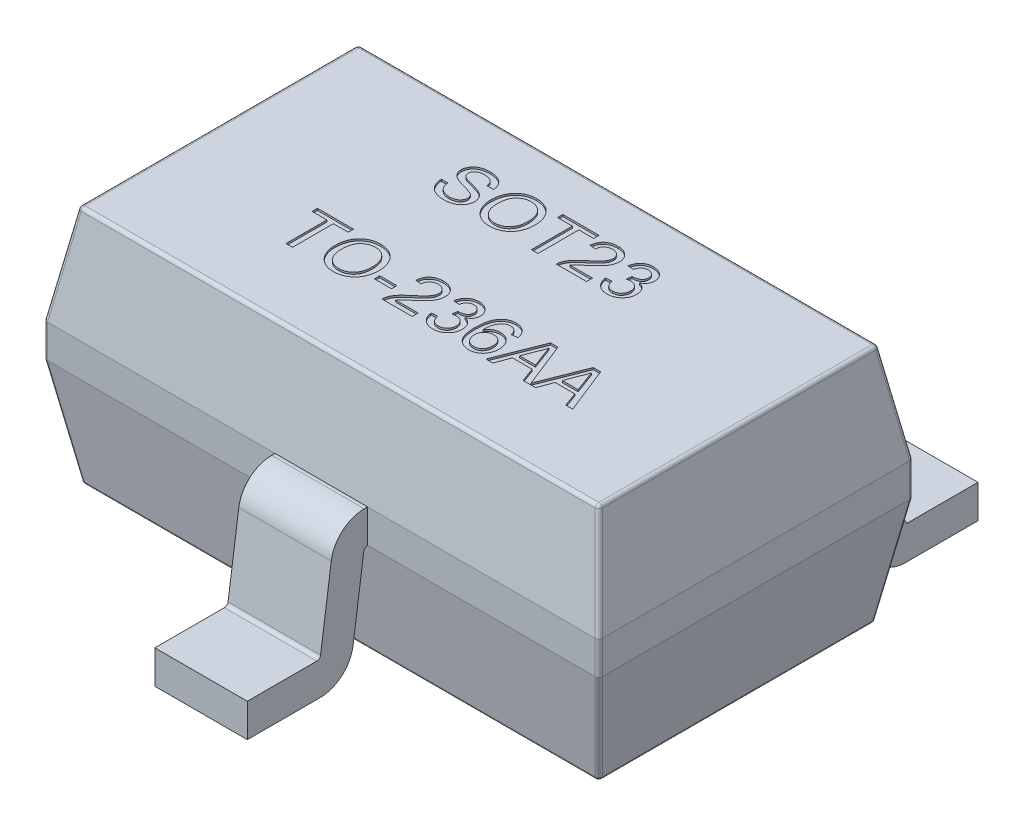
SolidWorks part; units mm, degrees
ref_plane "Front" through (0, 0, 0) normal (0, 0, 1) x (1, 0, 0)
ref_plane "Top" through (0, 0, 0) normal (0, 1, 0) x (1, 0, 0)
ref_plane "Right" through (0, 0, 0) normal (1, 0, 0) x (0, 0, -1)
ref_plane "Plane3" through (0, 0.585, 0) normal (0, 1, 0) x (-1, 0, 0)
sketch "Sketch5" plane through (0, 0.585, 0) normal (0, 1, 0) x (-1, 0, 0)
  line L0 (1.5, -0.85) -> (1.5, 0.85)
  line L1 (0, 0) -> (-1.5, 0) construction
  line L2 (0, 0) -> (0, 0.85) construction
  line L3 (1.5, 0.85) -> (-1.5, 0.85)
  line L4 (-1.5, -0.85) -> (-1.5, 0.85)
  line L5 (1.5, -0.85) -> (-1.5, -0.85)
  point P8 (1.5, 0)
  dimension "D1" = 1.5
  dimension "D2" = 0.85
extrude "Boss-Extrude3" add sketch "Sketch5" against normal blind 0.585 draft 10
sketch "Sketch6" plane through (0, 0.585, 0) normal (0, 1, 0) x (1, 0, 0)
  line L4 (1.5, -0.85) -> (1.5, 0.85)
  line L5 (1.5, 0.85) -> (-1.5, 0.85)
  line L6 (-1.5, 0.85) -> (-1.5, -0.85)
  line L7 (-1.5, -0.85) -> (1.5, -0.85)
  line L8 (1.5, -0.85) -> (1.5, 0.85)
  line L9 (1.5, 0.85) -> (-1.5, 0.85)
  line L10 (-1.5, 0.85) -> (-1.5, -0.85)
  line L11 (-1.5, -0.85) -> (1.5, -0.85)
  dimension "D1" = 0
extrude "Boss-Extrude4" add sketch "Sketch6" along normal blind 0.18
sketch "Sketch7" plane through (0, 0.765, 0) normal (0, 1, 0) x (1, 0, 0)
  line L4 (-1.5, -0.85) -> (1.5, -0.85)
  line L5 (1.5, -0.85) -> (1.5, 0.85)
  line L6 (1.5, 0.85) -> (-1.5, 0.85)
  line L7 (-1.5, 0.85) -> (-1.5, -0.85)
  line L8 (-1.5, -0.85) -> (1.5, -0.85)
  line L9 (1.5, -0.85) -> (1.5, 0.85)
  line L10 (1.5, 0.85) -> (-1.5, 0.85)
  line L11 (-1.5, 0.85) -> (-1.5, -0.85)
  dimension "D1" = 0
extrude "Boss-Extrude5" add sketch "Sketch7" along normal blind 0.535 draft 10
sketch "Sketch8" plane through (0, 0, 0) normal (1, 0, 0) x (0, 0, -1)
  line L0 (-0.85, 0.765) -> (-0.85, 0.585)
  line L1 (-0.85, 0.585) -> (-0.8504, 0.585)
  line L2 (4.9241, 0.585) -> (-4.9241, 0.585) construction
  line L3 (-0.7468, 0) -> (-0.85, 0.585) construction
  line L4 (-0.8702, 0.5678) -> (-0.9282, 0.1549)
  line L5 (-1.1065, 0) -> (-1.5, 0)
  line L6 (-1.5, 0) -> (-1.5, 0.18)
  line L7 (-0.85, 0.765) -> (-0.8678, 0.765)
  line L8 (-1.046, 0.6101) -> (-1.1041, 0.1972)
  line L9 (-1.1239, 0.18) -> (-1.5, 0.18)
  arc A0 (-0.9282, 0.1549) -> (-1.1065, 0) centre (-1.1065, 0.18) cw
  arc A1 (-0.8678, 0.765) -> (-1.046, 0.6101) centre (-0.8678, 0.585) ccw
  arc A2 (-0.8504, 0.585) -> (-0.8702, 0.5678) centre (-0.8504, 0.565) ccw
  arc A3 (-1.1041, 0.1972) -> (-1.1239, 0.18) centre (-1.1239, 0.2) cw
  point P13 (-0.95, 0)
  point P21 (-0.8678, 0.585)
  dimension "D9" = 0.18
  dimension "D10" = 0.18
  dimension "D11" = 0.02
  dimension "D12" = 0.02
  dimension "D1" = 0.18
  dimension "D2" = 1.5
  dimension "D3" = 0.18
  dimension "D4" = 0
  dimension "D5" = 0
  dimension "D6" = 0.55
  dimension "D7" = 98
  dimension "D8" = 0.65
extrude "Boss-Extrude6" add sketch "Sketch8" along normal blind 0.25 and the other way blind 0.25
ref_plane "Plane4" through (0.95, 0, 0) normal (1, 0, 0) x (0, 0, -1)
sketch "Sketch10" plane through (0.95, 0, 0) normal (1, 0, 0) x (0, 0, -1)
  line L0 (0, 0) -> (0, 1.6602) construction
  line L1 (0.85, 0.585) -> (0.85, 0.765)
  line L2 (0.8504, 0.585) -> (0.85, 0.585)
  line L3 (0.9282, 0.1549) -> (0.8702, 0.5678)
  line L4 (1.5, 0) -> (1.1065, 0)
  line L5 (1.5, 0.18) -> (1.5, 0)
  line L6 (1.1239, 0.18) -> (1.5, 0.18)
  line L7 (1.046, 0.6101) -> (1.1041, 0.1972)
  line L24 (0.85, 0.765) -> (0.8678, 0.765)
  arc A0 (0.8504, 0.585) -> (0.8702, 0.5678) centre (0.8504, 0.565) cw
  arc A1 (1.1065, 0) -> (0.9282, 0.1549) centre (1.1065, 0.18) cw
  arc A2 (1.1239, 0.18) -> (1.1041, 0.1972) centre (1.1239, 0.2) cw
  arc A3 (0.8678, 0.765) -> (1.046, 0.6101) centre (0.8678, 0.585) cw
extrude "Boss-Extrude8" add sketch "Sketch10" along normal blind 0.25 and the other way blind 0.25
pattern_linear "LPattern2" count 3 spacing 0.95 along (-1, 0, 0) skipping (1, 0) of "Boss-Extrude8"
sketch "Sketch11" plane through (0, 1.3, 0) normal (0, 1, 0) x (1, 0, 0)
  text T0 "  SOT23\r\nTO-236AA" font "Arial" height 0.25
extrude "Cut-Extrude1" cut sketch "Sketch11" against normal blind 0.01
fillet "Fillet1" radius 0.02 20 edges at (-1.4484, 0.2925, -0.7984) (-1.5, 0.675, -0.85) (-1.4528, 1.0325, -0.8028) (-1.4528, 1.0325, 0.8028) (-1.5, 0.675, 0.85) (-1.4484, 0.2925, 0.7984) (-1.3968, 0, 0) (0, 0, 0.7468) (0, 0, -0.7468) (1.3968, 0, 0) (1.4484, 0.2925, -0.7984) (1.5, 0.675, -0.85) (1.4528, 1.0325, -0.8028) (1.4484, 0.2925, 0.7984) (1.5, 0.675, 0.85) (1.4528, 1.0325, 0.8028) (1.4057, 1.3, 0) (0, 1.3, -0.7557) (-1.4057, 1.3, 0) (0, 1.3, 0.7557)
